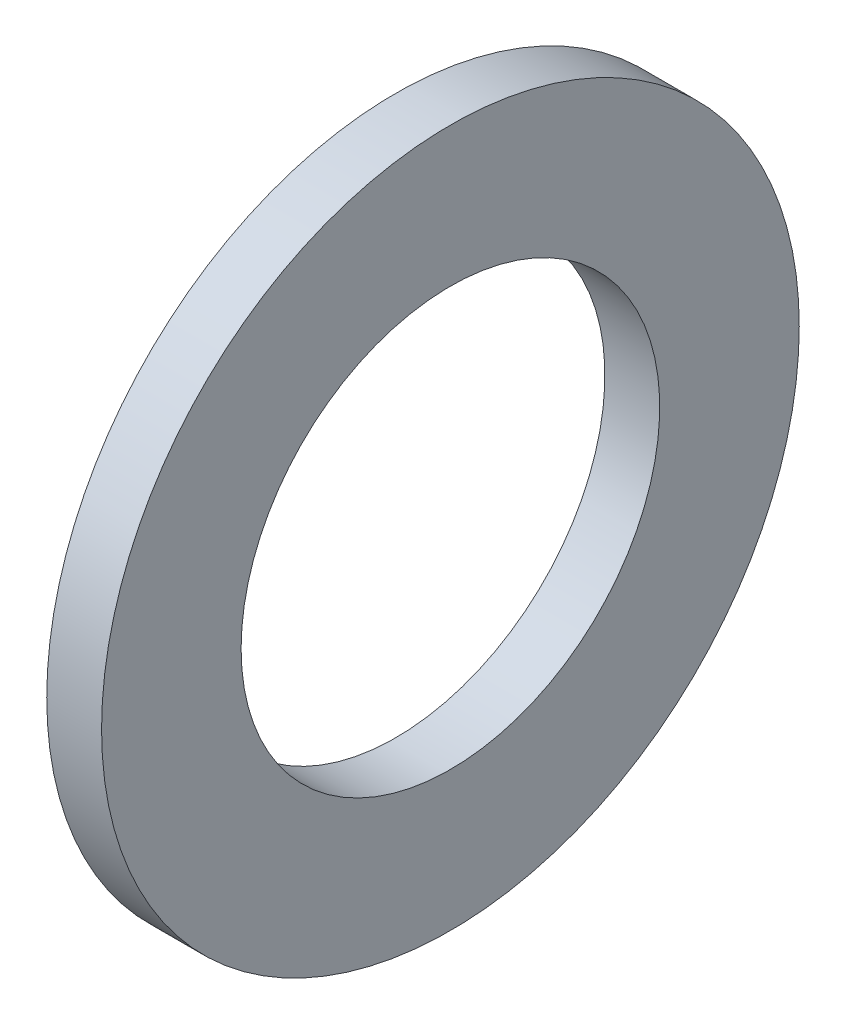
SolidWorks part; units mm, degrees
ref_plane "Front Plane" through (0, 0, 0) normal (0, 0, 1) x (1, 0, 0)
ref_plane "Top Plane" through (0, 0, 0) normal (0, 1, 0) x (1, 0, 0)
ref_plane "Right Plane" through (0, 0, 0) normal (1, 0, 0) x (0, 0, -1)
ref_plane "Plane1" through (0, 0, 0) normal (0, 0, 1) x (1, 0, 0)
sketch "Sketch1" plane through (0, 0, 0) normal (0, 0, 1) x (1, 0, 0)
  line L0 (-3.75, 10.5) -> (-1, 10.5)
  line L1 (-1, 10.5) -> (-1, 17.5)
  line L2 (-1, 17.5) -> (-3.75, 17.5)
  line L3 (-3.75, 17.5) -> (-3.75, 10.5)
  line L4 (50, 0) -> (-50, 0) construction
revolve "Revolve1" add sketch "Sketch1" angle 360 about L4
